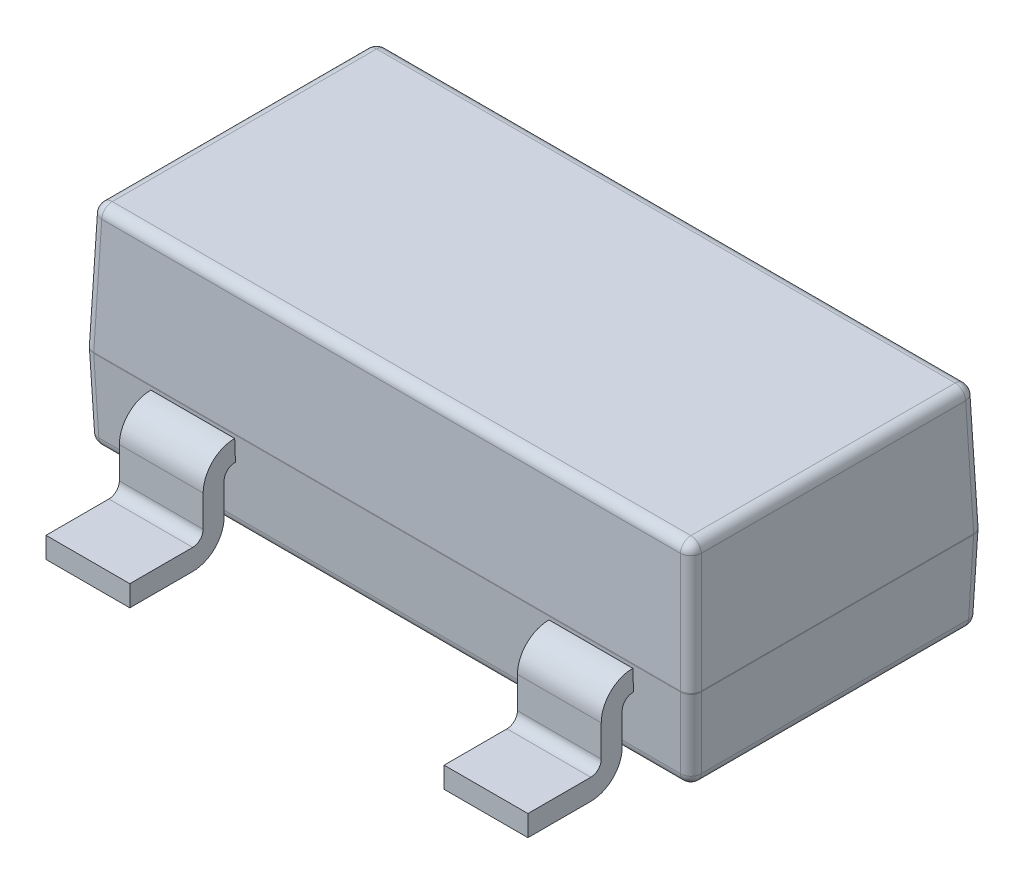
SolidWorks part; units mm, degrees
ref_plane "Front" through (0, 0, 0) normal (0, 0, 1) x (1, 0, 0)
ref_plane "Top" through (0, 0, 0) normal (0, 1, 0) x (1, 0, 0)
ref_plane "Right" through (0, 0, 0) normal (1, 0, 0) x (0, 0, -1)
sketch "Sketch1" plane through (0, 0, 0) normal (0, 1, 0) x (1, 0, 0)
  line L1 (-1.4723, 0.7036) -> (1.4277, 0.7036)
  line L2 (-1.4723, 0.7036) -> (-1.4723, -0.6964)
  line L3 (-1.4723, -0.6964) -> (1.4277, -0.6964)
  line L4 (1.4277, 0.7036) -> (1.4277, -0.6964)
  dimension "D1" = 2.9
  dimension "D2" = 1.4
extrude "Extrude1" add sketch "Sketch1" along normal blind 0.6 draft 2 and the other way blind 0.4 draft 2
fillet "Fillet1" radius 0.05 20 edges at (1.4067, 0.6, -0.0036) (-1.4584, -0.4, -0.0036) (-1.4654, -0.2, 0.6894) (-0.0223, -0.4, -0.6896) (-1.4654, -0.2, -0.6966) (1.4137, -0.4, -0.0036) (-0.0223, 0.6, -0.6826) (1.4207, -0.2, -0.6966) (-0.0223, -0.4, 0.6824) (1.4207, -0.2, 0.6894) (-1.4514, 0.6, -0.0036) (-0.0223, 0, -0.7036) (1.4277, 0, -0.0036) (-0.0223, 0, 0.6964) (-1.4723, 0, -0.0036) (-0.0223, 0.6, 0.6755) (-1.4619, 0.3, -0.6931) (1.4172, 0.3, -0.6931) (1.4172, 0.3, 0.6859) (-1.4619, 0.3, 0.6859)
sketch "Sketch2" plane through (0, 0, 0) normal (1, 0, 0) x (0, 0, -1)
  line L0 (0.7036, -0.0717) -> (0, -0.0717)
  line L1 (0.8036, -0.1717) -> (0.8036, -0.3217)
  line L2 (0.9036, -0.4217) -> (1.2036, -0.4217)
  line L3 (-0.6464, 0.0017) -> (0.6536, 0.0017) construction
  arc A0 (0.7036, -0.0717) -> (0.8036, -0.1717) centre (0.7036, -0.1717) cw
  arc A1 (0.8036, -0.3217) -> (0.9036, -0.4217) centre (0.9036, -0.3217) ccw
  point P2 (0.0036, 0.0017)
  point P11 (0.8036, -0.0717)
  point P14 (0.8036, -0.4217)
  dimension "D5" = 0.1
  dimension "D1" = 0.4
  dimension "D2" = 1.2
  dimension "D4" = 0.35
sketch "Sketch4" plane through (0, 0, 0) normal (0, 0, 1) x (1, 0, 0)
  line L1 (-0.2, -0.0217) -> (0.2, -0.0217)
  line L2 (-0.2, -0.0217) -> (-0.2, -0.1217)
  line L3 (-0.2, -0.1217) -> (0.2, -0.1217)
  line L4 (0.2, -0.0217) -> (0.2, -0.1217)
  dimension "D1" = 0.4
  dimension "D2" = 0.1
  dimension "D3" = 0.2
  dimension "D4" = 0.05
sweep "Sweep2" add profiles "Sketch4" path "Sketch2"
ref_plane "Plane1" through (0.95, 0, 0) normal (1, 0, 0) x (0, 0, -1)
sketch "Sketch5" plane through (0.95, 0, 0) normal (1, 0, 0) x (0, 0, -1)
  line L0 (0.0846, -0.0683) -> (-0.6964, -0.0683)
  line L1 (-0.7964, -0.1683) -> (-0.7964, -0.3183)
  line L2 (-0.8964, -0.4183) -> (-1.1964, -0.4183)
  line L3 (0.6536, -0.0017) -> (-0.6464, -0.0017) construction
  line L4 (-0.6464, 0.0017) -> (0.6536, 0.0017) construction
  arc A0 (-0.6964, -0.0683) -> (-0.7964, -0.1683) centre (-0.6964, -0.1683) ccw
  arc A1 (-0.7964, -0.3183) -> (-0.8964, -0.4183) centre (-0.8964, -0.3183) cw
  point P2 (0.0036, -0.0017)
  point P7 (0.0036, 0.0017)
  point P12 (-0.7964, -0.0683)
  point P15 (-0.7964, -0.4183)
  dimension "D5" = 0.1
  dimension "D1" = 0.8
  dimension "D2" = 0.4
  dimension "D3" = 0.35
  dimension "D4" = 0.07
sketch "Sketch6" plane through (0, 0, 0) normal (0, 0, 1) x (1, 0, 0)
  line L1 (0.75, -0.0183) -> (1.15, -0.0183)
  line L2 (0.75, -0.0183) -> (0.75, -0.1183)
  line L3 (0.75, -0.1183) -> (1.15, -0.1183)
  line L4 (1.15, -0.0183) -> (1.15, -0.1183)
  dimension "D1" = 0.4
  dimension "D2" = 0.1
  dimension "D3" = 0.2
  dimension "D4" = 0.05
sweep "Sweep3" add profiles "Sketch6" path "Sketch5"
pattern_linear "LPattern1" count 2 spacing 1.9 along (-1, 0, 0) of "Sweep3"
